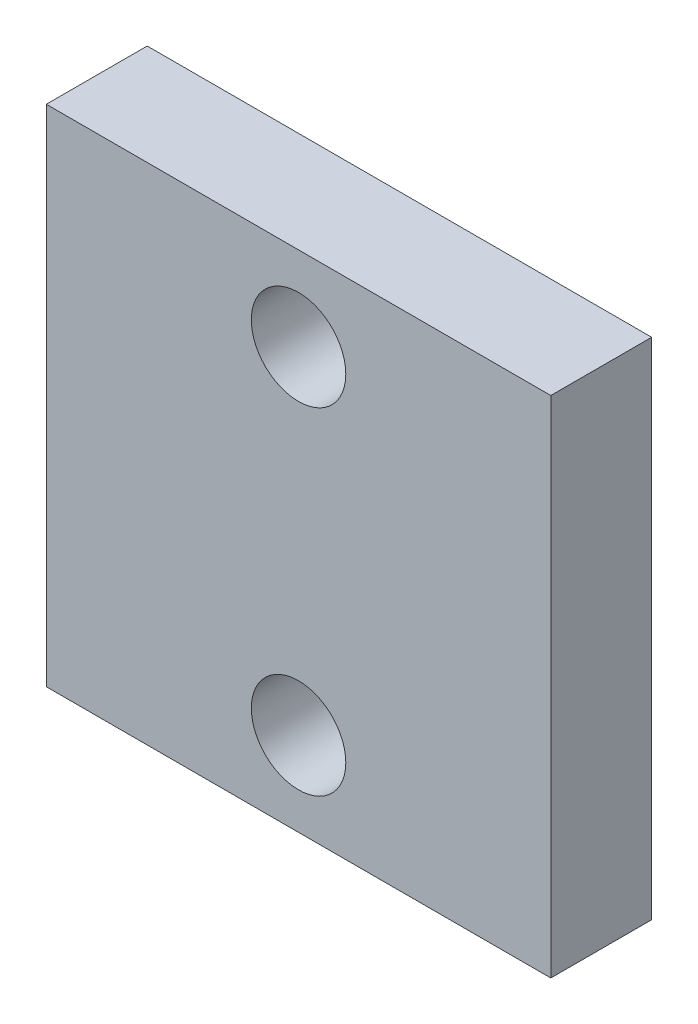
SolidWorks part; units mm, degrees
ref_plane "Plan de face" through (0, 0, 0) normal (0, 0, 1) x (1, 0, 0)
ref_plane "Plan de dessus" through (0, 0, 0) normal (0, 1, 0) x (1, 0, 0)
ref_plane "Plan de droite" through (0, 0, 0) normal (1, 0, 0) x (0, 0, -1)
sketch "Esquisse1" plane through (0, 0, 0) normal (0, 0, 1) x (1, 0, 0)
  line L5 (-30, -30) -> (30, -30)
  line L6 (-30, -30) -> (-30, 30)
  line L7 (-30, 30) -> (30, 30)
  line L8 (30, -30) -> (30, 30)
  line L9 (-30, -30) -> (30, 30) construction
  line L10 (-30, 30) -> (30, -30) construction
  circle A0 centre (0, 20) radius 5.6186
  circle A1 centre (0, -20) radius 5.6186
  point P0 (0, 0)
  point P10 (0, 17.8346)
  point P11 (0, -18.0931)
  point P12 (0, -30)
  point P13 (0, 21.4533)
  point P14 (0, -17.8346)
  point P16 (4.1356, 21.9702)
  dimension "D1" = 10
  dimension "D3" = 40
extrude "Boss.-Extru.2" add sketch "Esquisse1" along normal blind 12
